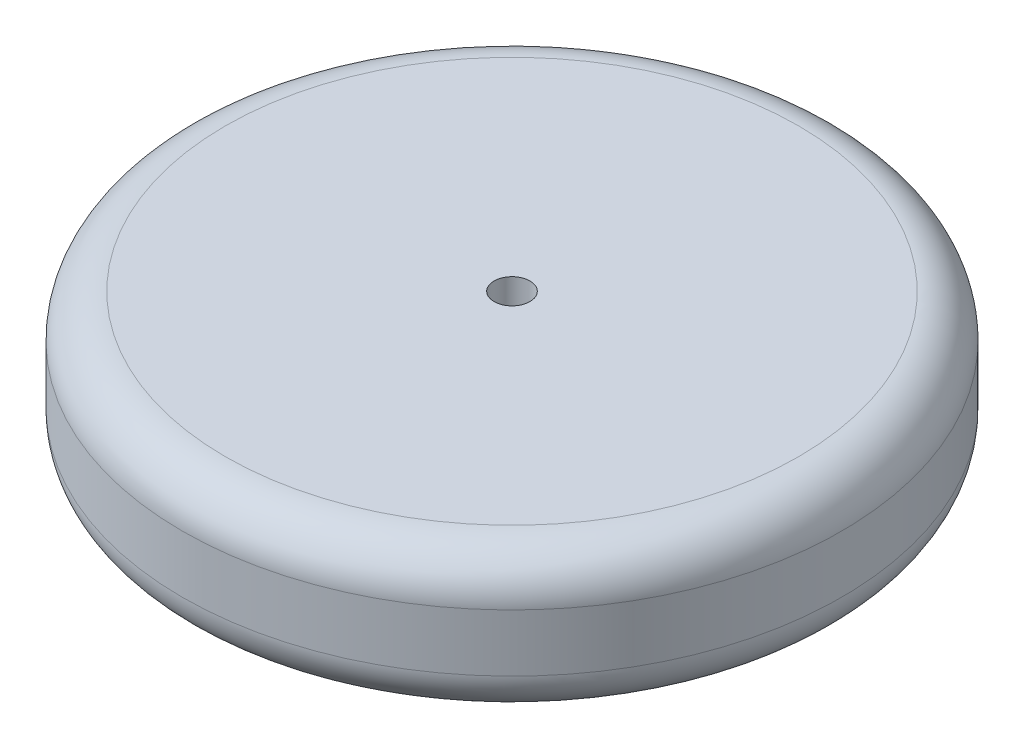
SolidWorks part; units mm, degrees
ref_plane "Front Plane" through (0, 0, 0) normal (0, 0, 1) x (1, 0, 0)
ref_plane "Top Plane" through (0, 0, 0) normal (0, 1, 0) x (1, 0, 0)
ref_plane "Right Plane" through (0, 0, 0) normal (1, 0, 0) x (0, 0, -1)
sketch "Sketch1" plane through (0, 0, 0) normal (0, 1, 0) x (1, 0, 0)
  circle A0 centre (0, 0) radius 292.1
  dimension "D1" = 584.2
extrude "Boss-Extrude1" add sketch "Sketch1" along normal blind 127
fillet "Fillet1" radius 38.1 2 edges at (0, 0, 292.1) (0, 127, 292.1)
sketch "Sketch2" plane through (0, 127, 0) normal (0, 1, 0) x (1, 0, 0)
  circle A0 centre (0, 0) radius 15.875
  dimension "D1" = 31.75
extrude "Cut-Extrude1" cut sketch "Sketch2" against normal through all
